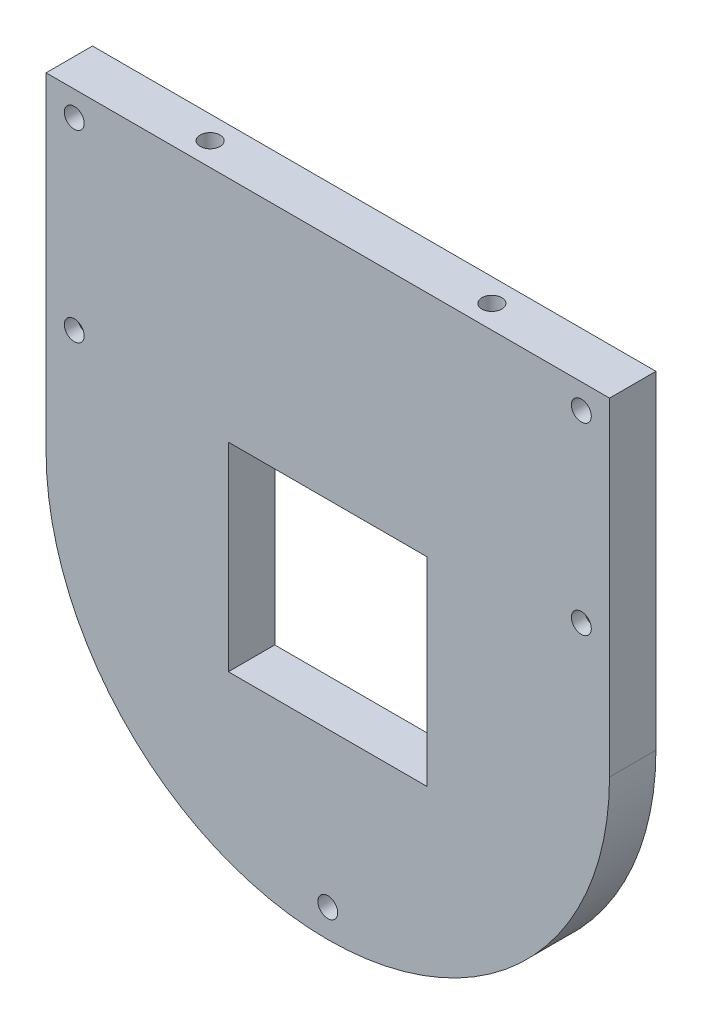
SolidWorks part; units mm, degrees
ref_plane "Front Plane" through (0, 0, 0) normal (0, 0, 1) x (1, 0, 0)
ref_plane "Top Plane" through (0, 0, 0) normal (0, 1, 0) x (1, 0, 0)
ref_plane "Right Plane" through (0, 0, 0) normal (1, 0, 0) x (0, 0, -1)
sketch "Sketch1" plane through (0, 0, 0) normal (0, 0, 1) x (1, 0, 0)
  line L1 (0, 0) -> (85, 0)
  line L2 (0, 0) -> (0, 95)
  line L3 (0, 95) -> (85, 95)
  line L4 (85, 0) -> (85, 95)
  dimension "D1" = 95
  dimension "D2" = 85
extrude "Boss-Extrude1" add sketch "Sketch1" along normal blind 7
sketch "Sketch2" plane through (0, 0, 7) normal (0, 0, 1) x (1, 0, 0)
  line L0 (0, 0) -> (85, 0) construction
  line L1 (27.5, 30) -> (57.5, 30)
  line L2 (27.5, 30) -> (27.5, 60)
  line L3 (27.5, 60) -> (57.5, 60)
  line L4 (57.5, 30) -> (57.5, 60)
  line L5 (27.5, 30) -> (57.5, 60) construction
  line L6 (27.5, 60) -> (57.5, 30) construction
  point P0 (42.5, 45)
  point P7 (42.5, 0)
  dimension "D1" = 0
  dimension "D2" = 30
  dimension "D3" = 30
  dimension "D4" = 45
extrude "Cut-Extrude1" cut sketch "Sketch2" against normal blind 7
sketch "Sketch4" plane through (0, 95, 0) normal (0, 1, 0) x (1, 0, 0)
  line L0 (0, -3.5) -> (85, -3.5) construction
  line L1 (0, -7) -> (0, 0) construction
  line L2 (85, -7) -> (85, 0) construction
  circle A0 centre (21.25, -3.5) radius 1.5
  circle A1 centre (63.75, -3.5) radius 1.5
  dimension "D1" = 3
  dimension "D2" = 3
  dimension "D3" = 21.25
  dimension "D4" = 21.25
extrude "Cut-Extrude2" cut sketch "Sketch4" against normal blind 10.5
sketch "Sketch6" plane through (0, 0, 0) normal (0, 0, -1) x (-1, 0, 0)
  line L0 (-85, 95) -> (0, 95) construction
  line L1 (-85, 0) -> (-85, 95) construction
  line L2 (-42.5, 60) -> (-42.5, 65.8033) construction
  line L3 (-57.5, 60) -> (-27.5, 60) construction
  line L4 (0, 95) -> (0, 0) construction
  line L5 (0, 0) -> (-85, 0) construction
  circle A0 centre (-80.75, 90.75) radius 1.5
  circle A1 centre (-4.25, 90.75) radius 1.5
  circle A2 centre (-4.45, 4.25) radius 1.5
  circle A3 centre (-80.75, 7.25) radius 1.5
  dimension "D1" = 3
  dimension "D5" = 3
  dimension "D7" = 3
  dimension "D2" = 4.25
  dimension "D3" = 4.25
  dimension "D4" = 4.45
  dimension "D6" = 4.25
  dimension "D8" = 7.25
  dimension "D9" = 4.25
extrude "Cut-Extrude3" cut sketch "Sketch6" against normal blind 8
sketch "Sketch7" plane through (0, 0, 0) normal (0, 0, -1) x (-1, 0, 0)
  line L0 (-85, 45) -> (-85, 0)
  line L1 (-85, 0) -> (0, 0)
  line L2 (0, 0) -> (0, 45)
  arc A0 (-85, 45) -> (0, 45) centre (-42.5, 45) ccw
  dimension "D1" = 85
extrude "Cut-Extrude4" cut sketch "Sketch7" against normal blind 10
sketch "Sketch8" plane through (0, 0, 7) normal (0, 0, 1) x (1, 0, 0)
  line L0 (85, 95) -> (0, 95) construction
  line L1 (85, 45) -> (85, 95) construction
  line L2 (42.5, 60) -> (42.5, 67.7032) construction
  line L3 (57.5, 60) -> (27.5, 60) construction
  circle A0 centre (80.75, 63) radius 1.5
  circle A1 centre (4.25, 63) radius 1.5
  dimension "D1" = 3
  dimension "D2" = 32
  dimension "D3" = 4.25
extrude "Cut-Extrude5" cut sketch "Sketch8" against normal blind 10
sketch "Sketch9" plane through (0, 0, 0) normal (0, 0, -1) x (-1, 0, 0)
  line L0 (-27.5, 30) -> (-57.5, 30) construction
  line L1 (-79.045, 65.9531) -> (-82.455, 65.9531)
  line L2 (-82.455, 65.9531) -> (-84.16, 63)
  line L3 (-84.16, 63) -> (-82.455, 60.0469)
  line L4 (-82.455, 60.0469) -> (-79.045, 60.0469)
  line L5 (-79.045, 60.0469) -> (-77.34, 63)
  line L6 (-77.34, 63) -> (-79.045, 65.9531)
  line L7 (-42.5, 60) -> (-42.5, 65.7072) construction
  line L8 (-57.5, 60) -> (-27.5, 60) construction
  line L9 (-0.84, 63) -> (-2.545, 60.0469)
  line L10 (-2.545, 65.9531) -> (-0.84, 63)
  line L11 (-5.955, 65.9531) -> (-2.545, 65.9531)
  line L12 (-7.66, 63) -> (-5.955, 65.9531)
  line L13 (-5.955, 60.0469) -> (-7.66, 63)
  line L14 (-2.545, 60.0469) -> (-5.955, 60.0469)
  circle A0 centre (-80.75, 63) radius 2.9531 construction
  dimension "D1" = 3.41
extrude "Cut-Extrude6" cut sketch "Sketch9" against normal blind 5
sketch "Sketch10" plane through (0, 0, 0) normal (0, 0, -1) x (-1, 0, 0)
  line L0 (-42.5, 2.5) -> (-42.5, 26.8409) construction
  arc A0 (-85, 45) -> (0, 45) centre (-42.5, 45) ccw construction
  circle A1 centre (-42.5, 6.75) radius 1.5
  dimension "D1" = 3
  dimension "D2" = 4.25
sketch "Sketch11" plane through (0, 0, 7) normal (0, 0, 1) x (1, 0, 0)
  circle A0 centre (42.5, 6.75) radius 1.5 construction
  circle A1 centre (42.5, 6.75) radius 1.5
extrude "Cut-Extrude8" cut sketch "Sketch11" against normal blind 4
sketch "Sketch12" plane through (0, 95, 0) normal (0, 1, 0) x (1, 0, 0)
  line L1 (0, -7) -> (85, -7)
  line L2 (0, -7) -> (0, 0)
  line L3 (0, 0) -> (85, 0)
  line L4 (85, -7) -> (85, 0)
extrude "Cut-Extrude9" cut sketch "Sketch12" against normal blind 0.5
